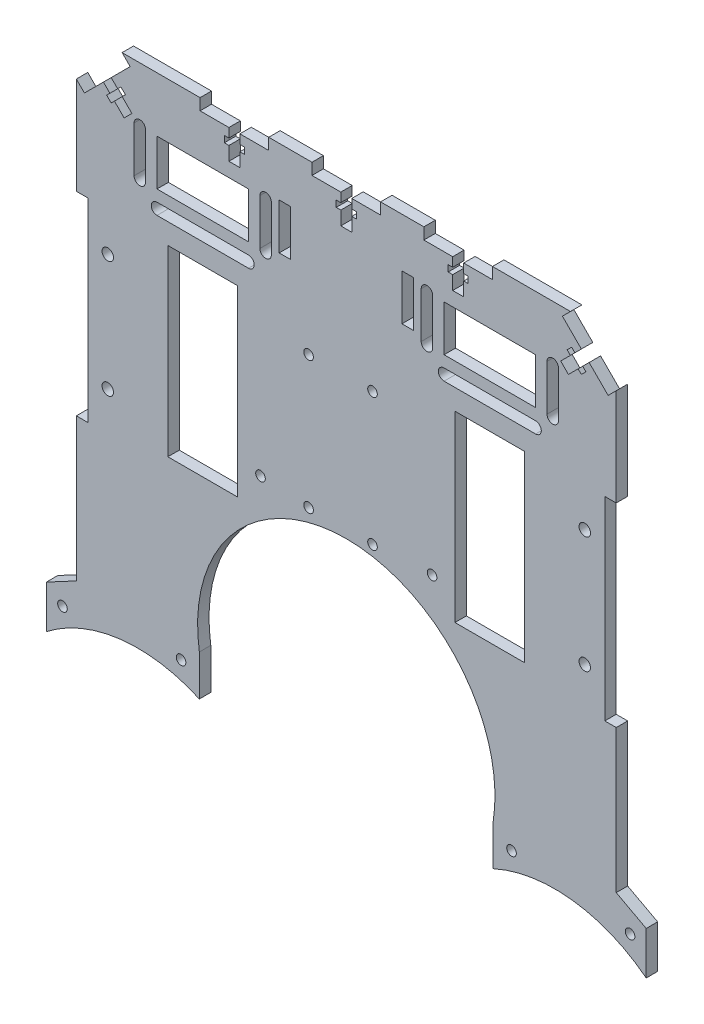
SolidWorks part; units mm, degrees
ref_plane "Front Plane" through (0, 0, 0) normal (0, 0, 1) x (1, 0, 0)
ref_plane "Top Plane" through (0, 0, 0) normal (0, 1, 0) x (1, 0, 0)
ref_plane "Right Plane" through (0, 0, 0) normal (1, 0, 0) x (0, 0, -1)
sketch "Sketch1" plane through (0, 0, 0) normal (0, 0, 1) x (1, 0, 0)
  line L0 (64.2262, -107) -> (118, -107)
  line L1 (-98, 103) -> (98, 103)
  line L3 (-118, -107) -> (-64.2262, -107)
  line L5 (-150, 100) -> (150, -100) construction
  line L6 (-150, -100) -> (150, 100) construction
  line L10 (0, 0) -> (0, 48.5738) construction
  line L12 (-47.5, 0) -> (47.5, 0) construction
  line L13 (47.5, -40) -> (47.5, 40)
  line L14 (47.5, 40) -> (78, 40)
  line L15 (78, 40) -> (78, -40)
  line L16 (78, -40) -> (47.5, -40)
  line L17 (-78, -40) -> (-47.5, -40)
  line L18 (-47.5, -40) -> (-47.5, 40)
  line L19 (-78, 40) -> (-78, -40)
  line L20 (-47.5, 40) -> (-78, 40)
  line L21 (78, 0) -> (118, 0) construction
  line L22 (118, 83) -> (118, -107)
  line L23 (-118, 83) -> (-118, -107)
  line L24 (-98, 103) -> (-98, 83) construction
  line L25 (-98, 83) -> (-118, 83) construction
  line L26 (0, 103) -> (0, -97) construction
  line L27 (-118, 83) -> (-98, 103)
  line L28 (98, 103) -> (118, 83)
  arc A0 (64.2262, -107) -> (-64.2262, -107) centre (0, -97) ccw
  point P0 (0, 0)
  point P19 (0, 0)
  point P22 (47.5, 0)
  point P33 (118, 0)
  dimension "D2" = 130
  dimension "D1" = 210
  dimension "D3" = 63
  dimension "D4" = 20
  dimension "D5" = 20
  dimension "D6" = 95
  dimension "D7" = 80
  dimension "D8" = 30.5
  dimension "D9" = 40
extrude "Boss-Extrude1" add sketch "Sketch1" along normal blind 5
sketch "Sketch4" plane through (0, 0, 5) normal (0, 0, 1) x (1, 0, 0)
  line L0 (-118, -2) -> (-113, -2) construction
  line L1 (-118, 83) -> (-118, -107) construction
  line L2 (-113, 40.5) -> (-113, -44.5)
  line L3 (-113, 40.5) -> (-118, 40.5)
  line L4 (-118, 40.5) -> (-118, -44.5)
  line L5 (-118, -44.5) -> (-113, -44.5)
  line L6 (0, 103) -> (0, 94.0884) construction
  line L7 (98, 103) -> (-98, 103) construction
  line L8 (118, -2) -> (113, -2) construction
  line L9 (118, -44.5) -> (113, -44.5)
  line L10 (118, 40.5) -> (118, -44.5)
  line L11 (113, 40.5) -> (118, 40.5)
  line L12 (113, 40.5) -> (113, -44.5)
  point P7 (-113, -2)
  point P20 (113, -2)
  dimension "D1" = 5
  dimension "D2" = 85
extrude "Cut-Extrude3" cut sketch "Sketch4" against normal through all
sketch "Sketch5" plane through (0, 0, 0) normal (0, 0, -1) x (-1, 0, 0)
  circle A0 centre (-104.25, 23.5) radius 2.5
  circle A1 centre (-104.25, -27.5) radius 2.5
  circle A2 centre (104.25, 23.5) radius 2.5
  circle A3 centre (104.25, -27.5) radius 2.5
extrude "Cut-Extrude4" cut sketch "Sketch5" against normal through all
sketch "Sketch7" plane through (0, 0, 5) normal (0, 0, 1) x (1, 0, 0)
  line L0 (98, 103) -> (-98, 103) construction
  line L1 (-15, 98) -> (-2.4, 98)
  line L2 (-15, 98) -> (-15, 103)
  line L3 (-15, 103) -> (15, 103)
  line L4 (15, 98) -> (15, 103)
  line L5 (-15, 98) -> (15, 103) construction
  line L6 (-15, 103) -> (15, 98) construction
  line L7 (15, 98) -> (15, 103) construction
  line L8 (0, 98) -> (0, 79.0269) construction
  line L9 (2.4, 98) -> (2.4, 94)
  line L10 (2.4, 94) -> (4.4, 94)
  line L11 (4.4, 94) -> (4.4, 91.2)
  line L12 (4.4, 91.2) -> (2.4, 91.2)
  line L13 (2.4, 91.2) -> (2.4, 85.2)
  line L14 (-2.4, 91.2) -> (-2.4, 85.2)
  line L15 (-4.4, 91.2) -> (-2.4, 91.2)
  line L16 (-4.4, 94) -> (-4.4, 91.2)
  line L17 (-2.4, 94) -> (-4.4, 94)
  line L18 (-2.4, 98) -> (-2.4, 94)
  line L19 (-2.4, 85.2) -> (2.4, 85.2)
  line L20 (2.4, 98) -> (15, 98)
  line L21 (-63.9151, 98) -> (-33.9151, 98) construction
  line L22 (-48.9151, 80.824) -> (0, 80.824) construction
  line L23 (-24.4575, 80.824) -> (-24.4575, 85.2) construction
  line L24 (-48.9151, 98) -> (-48.9151, 80.824) construction
  line L25 (-33.9151, 103) -> (-63.9151, 98) construction
  line L42 (-33.9151, 98) -> (-63.9151, 103) construction
  line L43 (-51.3151, 98) -> (-63.9151, 98)
  line L60 (-118, 83) -> (-114.4614, 79.4675) construction
  line L61 (-117.997, 83.003) -> (-114.4614, 79.4675) construction
  line L62 (-114.4614, 79.4675) -> (-104.463, 89.466) construction
  line L63 (-104.463, 89.466) -> (-95.1873, 80.1903) construction
  line L64 (-102.7659, 91.163) -> (-99.9375, 88.3346)
  line L65 (-100.9274, 93.0015) -> (-102.978, 90.9509) construction
  line L66 (-99.9375, 88.3346) -> (-98.5233, 89.7488)
  line L67 (-98.5233, 89.7488) -> (-96.5434, 87.7689)
  line L68 (-96.5434, 87.7689) -> (-97.9576, 86.3547)
  line L69 (-97.9576, 86.3547) -> (-93.7149, 82.1121)
  line L70 (-101.3517, 82.9606) -> (-97.109, 78.718)
  line L71 (-102.7659, 81.5464) -> (-101.3517, 82.9606)
  line L72 (-104.7458, 83.5263) -> (-102.7659, 81.5464)
  line L73 (-103.3316, 84.9405) -> (-104.7458, 83.5263)
  line L74 (-106.16, 87.7689) -> (-103.3316, 84.9405)
  line L75 (-106.16, 87.7689) -> (-102.7659, 91.163)
  line L76 (-93.7149, 82.1121) -> (-97.109, 78.718)
  line L77 (104.463, 89.466) -> (95.1873, 80.1903) construction
  line L78 (93.7149, 82.1121) -> (97.109, 78.718)
  line L79 (106.16, 87.7689) -> (102.7659, 91.163)
  line L80 (106.16, 87.7689) -> (103.3316, 84.9405)
  line L81 (103.3316, 84.9405) -> (104.7458, 83.5263)
  line L82 (104.7458, 83.5263) -> (102.7659, 81.5464)
  line L83 (102.7659, 81.5464) -> (101.3517, 82.9606)
  line L84 (101.3517, 82.9606) -> (97.109, 78.718)
  line L85 (97.9576, 86.3547) -> (93.7149, 82.1121)
  line L86 (96.5434, 87.7689) -> (97.9576, 86.3547)
  line L87 (98.5233, 89.7488) -> (96.5434, 87.7689)
  line L88 (99.9375, 88.3346) -> (98.5233, 89.7488)
  line L89 (102.7659, 91.163) -> (99.9375, 88.3346)
  line L90 (-63.9151, 98) -> (-63.9151, 103)
  line L91 (-33.9151, 103) -> (-63.9151, 103)
  line L92 (-46.5151, 85.2) -> (-51.3151, 85.2)
  line L93 (-46.5151, 98) -> (-46.5151, 94)
  line L94 (-46.5151, 94) -> (-44.5151, 94)
  line L95 (-44.5151, 94) -> (-44.5151, 91.2)
  line L96 (-44.5151, 91.2) -> (-46.5151, 91.2)
  line L97 (-46.5151, 91.2) -> (-46.5151, 85.2)
  line L98 (-51.3151, 91.2) -> (-51.3151, 85.2)
  line L99 (-53.3151, 91.2) -> (-51.3151, 91.2)
  line L100 (-53.3151, 94) -> (-53.3151, 91.2)
  line L101 (-51.3151, 94) -> (-53.3151, 94)
  line L102 (-51.3151, 98) -> (-51.3151, 94)
  line L103 (-33.9151, 98) -> (-33.9151, 103)
  line L104 (-33.9151, 98) -> (-46.5151, 98)
  line L105 (33.9151, 98) -> (63.9151, 103) construction
  line L106 (33.9151, 103) -> (63.9151, 98) construction
  line L107 (63.9151, 98) -> (33.9151, 98) construction
  line L108 (33.9151, 98) -> (46.5151, 98)
  line L109 (33.9151, 98) -> (33.9151, 103)
  line L110 (51.3151, 98) -> (51.3151, 94)
  line L111 (51.3151, 94) -> (53.3151, 94)
  line L112 (53.3151, 94) -> (53.3151, 91.2)
  line L113 (53.3151, 91.2) -> (51.3151, 91.2)
  line L114 (51.3151, 91.2) -> (51.3151, 85.2)
  line L115 (46.5151, 91.2) -> (46.5151, 85.2)
  line L116 (44.5151, 91.2) -> (46.5151, 91.2)
  line L117 (44.5151, 94) -> (44.5151, 91.2)
  line L118 (46.5151, 94) -> (44.5151, 94)
  line L119 (46.5151, 98) -> (46.5151, 94)
  line L120 (46.5151, 85.2) -> (51.3151, 85.2)
  line L121 (33.9151, 103) -> (63.9151, 103)
  line L122 (63.9151, 98) -> (63.9151, 103)
  line L123 (51.3151, 98) -> (63.9151, 98)
  point P4 (0, 100.5)
  point P47 (-48.9151, 100.5)
  point P64 (48.9151, 100.5)
  dimension "D1" = 2.4
  dimension "D2" = 4
  dimension "D3" = 2.8
  dimension "D4" = 2
  dimension "D5" = 6
  dimension "D6" = 2.4
  dimension "D7" = 4
  dimension "D8" = 2.8
  dimension "D9" = 2
  dimension "D10" = 6
  dimension "D11" = 2.4
  dimension "D12" = 2.4
extrude "Cut-Extrude6" cut sketch "Sketch7" against normal through all
sketch "Sketch8" plane through (0, 0, 5) normal (0, 0, 1) x (1, 0, 0)
  line L0 (-47.5, -40) -> (-47.5, -27) construction
  line L1 (-47.5, -40) -> (-47.5, 40) construction
  line L2 (-47.5, -27) -> (-37.5, -27) construction
  line L3 (0, 0) -> (0, -8.9641) construction
  circle A0 centre (-37.5, -27) radius 2.1
  circle A1 centre (37.5, -27) radius 2.1
  dimension "D3" = 4.2
  dimension "D1" = 13
  dimension "D2" = 10
extrude "Cut-Extrude7" cut sketch "Sketch8" against normal through all
sketch "Sketch9" plane through (0, 0, 5) normal (0, 0, 1) x (1, 0, 0)
  line L0 (94.4675, 99.4614) -> (98, 103)
  line L1 (98, 103) -> (118, 83)
  line L2 (118, 83) -> (114.4645, 79.4645)
  line L3 (114.4645, 79.4645) -> (94.4675, 99.4614)
  line L4 (-118, 83) -> (-114.4614, 79.4675)
  line L5 (-114.4614, 79.4675) -> (-94.4645, 99.4645)
  line L6 (-94.4645, 99.4645) -> (-98, 103)
  line L7 (-98, 103) -> (-118, 83)
extrude "Cut-Extrude8" cut sketch "Sketch9" against normal blind 5
sketch "Sketch10" plane through (0, 0, 5) normal (0, 0, 1) x (1, 0, 0)
  line L0 (-62.75, 40) -> (-62.75, 98) construction
  line L1 (-47.5, 40) -> (-78, 40) construction
  line L2 (-63.9151, 98) -> (-51.3151, 98) construction
  line L3 (0, 85.2) -> (0, 74.9993) construction
  line L4 (-2.4, 85.2) -> (2.4, 85.2) construction
  line L5 (42.75, 79) -> (42.75, 59)
  line L6 (-82.75, 79) -> (-42.75, 79)
  line L7 (-82.75, 79) -> (-82.75, 59)
  line L8 (-82.75, 59) -> (-42.75, 59)
  line L9 (-42.75, 79) -> (-42.75, 59)
  line L10 (-82.75, 79) -> (-42.75, 59) construction
  line L11 (-82.75, 59) -> (-42.75, 79) construction
  line L12 (82.75, 59) -> (42.75, 59)
  line L13 (82.75, 79) -> (82.75, 59)
  line L14 (82.75, 79) -> (42.75, 79)
  line L15 (-82.75, 51.5) -> (-42.75, 51.5) construction
  line L16 (-82.75, 54) -> (-42.75, 54)
  line L17 (-82.75, 49) -> (-42.75, 49)
  line L18 (-42.75, 69) -> (-35.25, 69) construction
  line L19 (-35.25, 79) -> (-35.25, 59) construction
  line L20 (-32.75, 79) -> (-32.75, 59)
  line L21 (-37.75, 79) -> (-37.75, 59)
  line L22 (-90.25, 79) -> (-90.25, 59) construction
  line L23 (-92.75, 79) -> (-92.75, 59)
  line L24 (-87.75, 79) -> (-87.75, 59)
  line L25 (82.75, 51.5) -> (42.75, 51.5) construction
  line L26 (82.75, 54) -> (42.75, 54)
  line L27 (82.75, 49) -> (42.75, 49)
  line L28 (35.25, 79) -> (35.25, 59) construction
  line L29 (32.75, 79) -> (32.75, 59)
  line L30 (37.75, 79) -> (37.75, 59)
  line L31 (90.25, 79) -> (90.25, 59) construction
  line L32 (92.75, 79) -> (92.75, 59)
  line L33 (87.75, 79) -> (87.75, 59)
  arc A0 (-82.75, 54) -> (-82.75, 49) centre (-82.75, 51.5) ccw
  arc A1 (-42.75, 49) -> (-42.75, 54) centre (-42.75, 51.5) ccw
  arc A2 (-32.75, 79) -> (-37.75, 79) centre (-35.25, 79) ccw
  arc A3 (-37.75, 59) -> (-32.75, 59) centre (-35.25, 59) ccw
  arc A4 (-92.75, 79) -> (-87.75, 79) centre (-90.25, 79) cw
  arc A5 (-87.75, 59) -> (-92.75, 59) centre (-90.25, 59) cw
  arc A6 (82.75, 54) -> (82.75, 49) centre (82.75, 51.5) cw
  arc A7 (42.75, 49) -> (42.75, 54) centre (42.75, 51.5) cw
  arc A8 (32.75, 79) -> (37.75, 79) centre (35.25, 79) cw
  arc A9 (37.75, 59) -> (32.75, 59) centre (35.25, 59) cw
  arc A10 (92.75, 79) -> (87.75, 79) centre (90.25, 79) ccw
  arc A11 (87.75, 59) -> (92.75, 59) centre (90.25, 59) ccw
  point P11 (-62.75, 69)
  point P22 (-62.75, 51.5)
  point P31 (-35.25, 69)
  point P38 (-90.25, 69)
  point P45 (62.75, 51.5)
  point P52 (35.25, 69)
  point P59 (90.25, 69)
  dimension "D1" = 20
  dimension "D2" = 40
  dimension "D3" = 5
  dimension "D4" = 5
  dimension "D5" = 5
  dimension "D6" = 5
extrude "Cut-Extrude9" cut sketch "Sketch10" against normal through all
sketch "Sketch13" plane through (0, 0, 5) normal (0, 0, 1) x (1, 0, 0)
  line L0 (-29.334, 81.5464) -> (-29.334, 61.5)
  line L1 (-29.334, 61.5) -> (-24.334, 61.5)
  line L2 (-24.334, 61.5) -> (-24.334, 45) construction
  line L3 (-24.334, 61.5) -> (-24.334, 81.5464)
  line L4 (-24.334, 81.5464) -> (-29.334, 81.5464)
  line L5 (0, 85.2) -> (0, 63.3803) construction
  line L6 (-2.4, 85.2) -> (2.4, 85.2) construction
  line L7 (24.334, 81.5464) -> (29.334, 81.5464)
  line L8 (24.334, 61.5) -> (24.334, 81.5464)
  line L9 (29.334, 61.5) -> (24.334, 61.5)
  line L10 (29.334, 81.5464) -> (29.334, 61.5)
extrude "Cut-Extrude10" cut sketch "Sketch13" against normal blind 10
sketch "Sketch14" plane through (0, 0, 0) normal (0, 0, -1) x (-1, 0, 0)
  line L0 (131.1131, -114) -> (118, -107) construction
  line L1 (131.1131, -132.7652) -> (131.1131, -114) construction
  line L2 (64.2262, -107) -> (64.2262, -124.8215) construction
  line L3 (131.1131, -114) -> (118, -107)
  line L4 (131.1131, -132.7652) -> (131.1131, -114)
  line L5 (64.2262, -107) -> (64.2262, -124.8215)
  line L6 (64.2262, -107) -> (118, -107)
  line L7 (0, -107) -> (0, -121.9873) construction
  line L8 (118, -107) -> (-118, -107) construction
  line L9 (-64.2262, -107) -> (-118, -107)
  line L10 (-64.2262, -107) -> (-64.2262, -124.8215)
  line L11 (-131.1131, -132.7652) -> (-131.1131, -114)
  line L12 (-131.1131, -114) -> (-118, -107)
  arc A0 (131.1131, -132.7652) -> (64.2262, -124.8215) centre (91.1131, -184) ccw construction
  arc A1 (131.1131, -132.7652) -> (64.2262, -124.8215) centre (91.1131, -184) ccw
  arc A2 (-131.1131, -132.7652) -> (-64.2262, -124.8215) centre (-91.1131, -184) cw
extrude "Boss-Extrude2" add sketch "Sketch14" against normal blind 5
sketch "Sketch16" plane through (0, 0, 5) normal (0, 0, 1) x (1, 0, 0)
  circle A0 centre (124.0554, -119.6157) radius 2.1
  circle A1 centre (72.2281, -114) radius 2.1
  circle A2 centre (-72.2281, -114) radius 2.1
  circle A3 centre (-124.0554, -119.6157) radius 2.1
extrude "Cut-Extrude12" cut sketch "Sketch16" against normal blind 10
sketch "Sketch17" plane through (0, 0, 5) normal (0, 0, 1) x (1, 0, 0)
  circle A0 centre (-16.4645, 29.4645) radius 2.1
  circle A1 centre (11.4645, 29.4645) radius 2.1
  circle A2 centre (11.4645, -28.4645) radius 2.1
  circle A3 centre (-16.4645, -28.4645) radius 2.1
extrude "Cut-Extrude13" cut sketch "Sketch17" against normal through all
